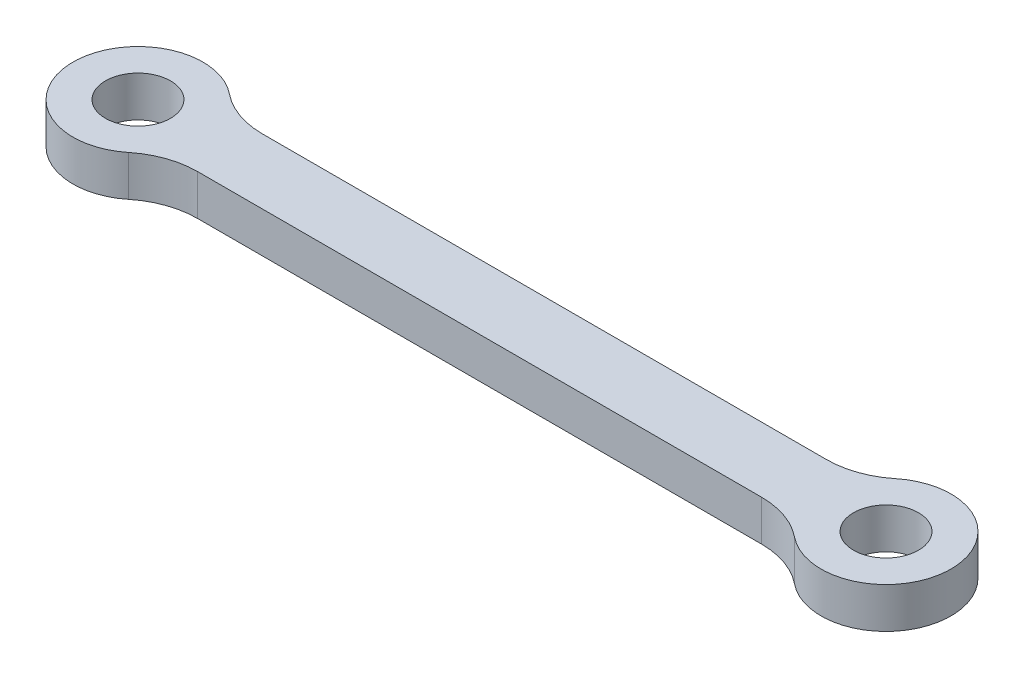
SolidWorks part; units mm, degrees
material "Epoxy, Unfilled"
ref_plane "Front Plane" through (0, 0, 0) normal (0, 0, 1) x (1, 0, 0)
ref_plane "Top Plane" through (0, 0, 0) normal (0, 1, 0) x (1, 0, 0)
ref_plane "Right Plane" through (0, 0, 0) normal (1, 0, 0) x (0, 0, -1)
sketch "Sketch1" plane through (0, 0, 0) normal (0, 1, 0) x (1, 0, 0)
  line L0 (0, 0) -> (0, 4) construction
  line L1 (0, 0) -> (-46, 0) construction
  line L3 (39.0718, -4) -> (-39.0718, -4)
  line L5 (39.0718, 4) -> (-39.0718, 4)
  circle A0 centre (-46, 0) radius 4
  arc A1 (-39.0718, 4) -> (-39.0718, -4) centre (-46, 0) ccw
  arc A2 (39.0718, 4) -> (39.0718, -4) centre (46, 0) cw
  circle A3 centre (46, 0) radius 4
  point P6 (-23, 0)
  point P15 (23, 0)
  dimension "D1" = 8
  dimension "D2" = 16
  dimension "D3" = 46
  dimension "D4" = 8
extrude "Boss-Extrude1" add sketch "Sketch1" along normal blind 5
fillet "Fillet1" radius 10 4 edges at (39.0718, 2.5, 4) (39.0718, 2.5, -4) (-39.0718, 2.5, -4) (-39.0718, 2.5, 4)
scale "Scale1" scale about centroid uniform scaling yes scale factor 0.5
